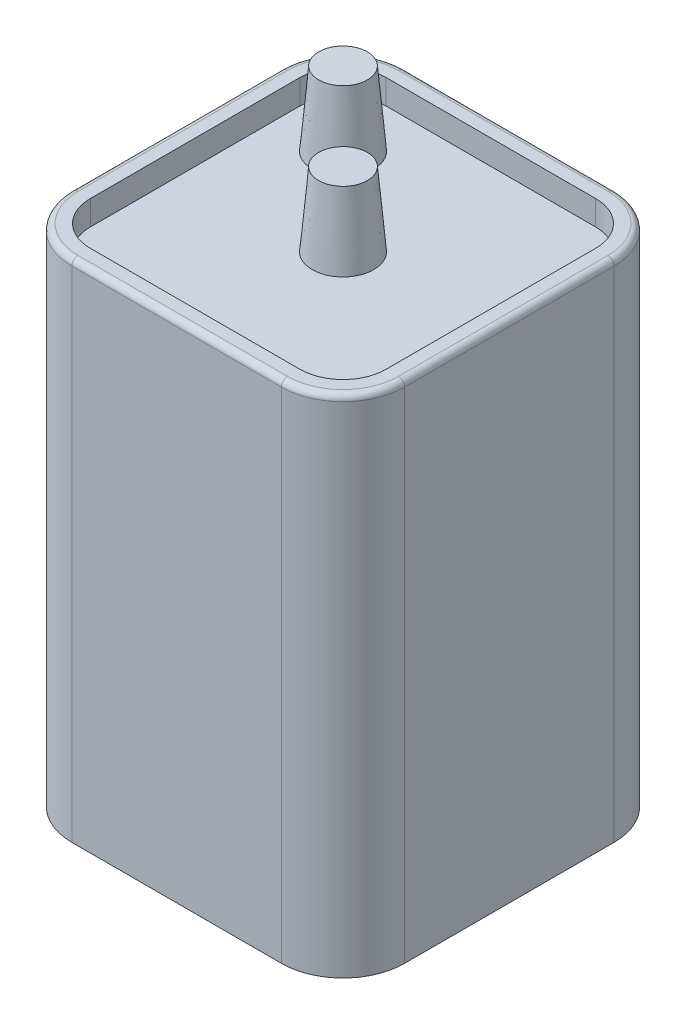
SolidWorks part; units mm, degrees
ref_plane "Front Plane" through (0, 0, 0) normal (0, 0, 1) x (1, 0, 0)
ref_plane "Top Plane" through (0, 0, 0) normal (0, 1, 0) x (1, 0, 0)
ref_plane "Right Plane" through (0, 0, 0) normal (1, 0, 0) x (0, 0, -1)
sketch "Sketch1" plane through (0, 0, 0) normal (0, 1, 0) x (1, 0, 0)
  line L1 (-34.29, -34.29) -> (34.29, -34.29)
  line L2 (-34.29, -34.29) -> (-34.29, 34.29)
  line L3 (-34.29, 34.29) -> (34.29, 34.29)
  line L4 (34.29, -34.29) -> (34.29, 34.29)
  line L5 (-34.29, -34.29) -> (34.29, 34.29) construction
  line L6 (-34.29, 34.29) -> (34.29, -34.29) construction
  point P0 (0, 0)
  dimension "D1" = 68.58
  dimension "D2" = 68.58
extrude "Base Extrude" add sketch "Sketch1" along normal blind 104.14
fillet "Side Fillets " radius 12.7 4 edges at (-34.29, 52.07, 34.29) (-34.29, 52.07, -34.29) (34.29, 52.07, -34.29) (34.29, 52.07, 34.29)
sketch "Sketch2" plane through (0, 104.14, 0) normal (0, 1, 0) x (1, 0, 0)
  line L8 (-30.48, 21.59) -> (-30.48, -21.59)
  line L9 (-21.59, -30.48) -> (21.59, -30.48)
  line L10 (30.48, -21.59) -> (30.48, 21.59)
  line L11 (21.59, 30.48) -> (-21.59, 30.48)
  line L12 (-30.48, 21.59) -> (-30.48, -21.59)
  line L13 (-21.59, -30.48) -> (21.59, -30.48)
  line L14 (30.48, -21.59) -> (30.48, 21.59)
  line L15 (21.59, 30.48) -> (-21.59, 30.48)
  arc A8 (-30.48, -21.59) -> (-21.59, -30.48) centre (-21.59, -21.59) ccw
  arc A9 (21.59, -30.48) -> (30.48, -21.59) centre (21.59, -21.59) ccw
  arc A10 (30.48, 21.59) -> (21.59, 30.48) centre (21.59, 21.59) ccw
  arc A11 (-21.59, 30.48) -> (-30.48, 21.59) centre (-21.59, 21.59) ccw
  arc A12 (-30.48, -21.59) -> (-21.59, -30.48) centre (-21.59, -21.59) ccw
  arc A13 (21.59, -30.48) -> (30.48, -21.59) centre (21.59, -21.59) ccw
  arc A14 (30.48, 21.59) -> (21.59, 30.48) centre (21.59, 21.59) ccw
  arc A15 (-21.59, 30.48) -> (-30.48, 21.59) centre (-21.59, 21.59) ccw
  dimension "D1" = 3.81
extrude "Top Cut " cut sketch "Sketch2" against normal blind 5.08
fillet "Top Face Fillet" radius 1.27 8 edges at (30.5703, 104.14, -30.5703) (34.29, 104.14, 0) (30.5703, 104.14, 30.5703) (0, 104.14, 34.29) (-30.5703, 104.14, 30.5703) (-34.29, 104.14, 0) (-30.5703, 104.14, -30.5703) (0, 104.14, -34.29)
sketch "Sketch-TERMINALS" plane through (0, 99.06, 0) normal (0, 1, 0) x (1, 0, 0)
  line L0 (-17.9605, 17.9605) -> (0, 0) construction
  line L1 (0, -37.719) -> (0, 37.719) construction
  circle A0 centre (0, 0) radius 6.35
  circle A1 centre (-17.9605, 17.9605) radius 6.35
  dimension "D1" = 12.7
  dimension "D2" = 25.4
  dimension "D3" = 45
extrude "Terminals" add sketch "Sketch-TERMINALS" along normal blind 15.24 draft 5
